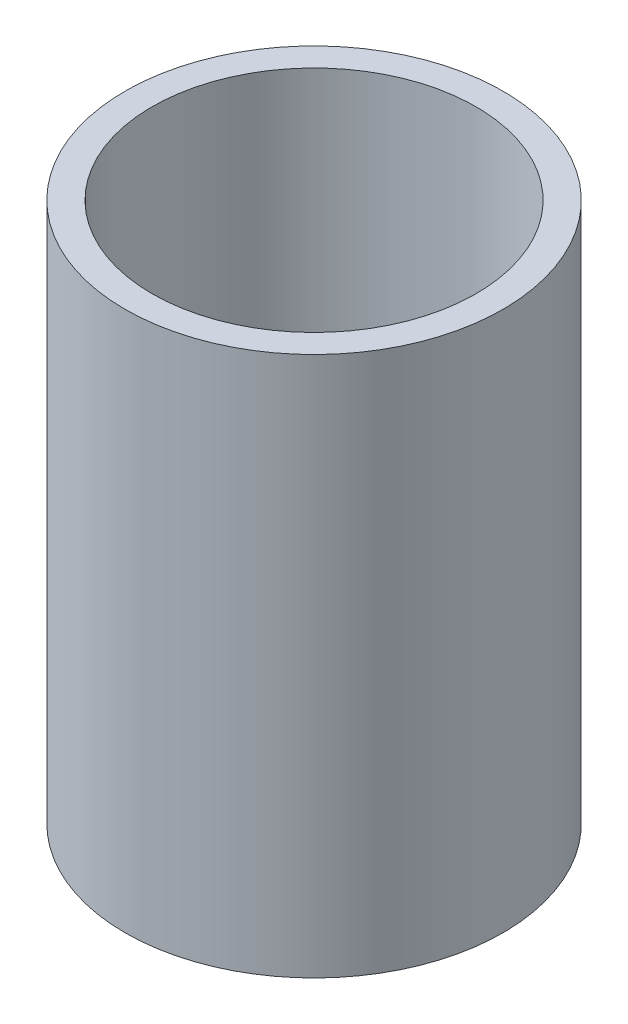
SolidWorks part; units mm, degrees
material "AISI 1035 钢 (SS)"
ref_plane "前视基准面" through (0, 0, 0) normal (0, 0, 1) x (1, 0, 0)
ref_plane "上视基准面" through (0, 0, 0) normal (0, 1, 0) x (1, 0, 0)
ref_plane "右视基准面" through (0, 0, 0) normal (1, 0, 0) x (0, 0, -1)
sketch "草图2" plane through (0, 0, 0) normal (0, 0, 1) x (1, 0, 0)
  line L1 (17.5, 0) -> (17.5, -50)
  line L4 (17.5, 0) -> (15, 0)
  line L5 (15, 0) -> (15, -50)
  line L6 (15, -50) -> (17.5, -50)
  line L7 (0, 0) -> (0, -50) construction
  dimension "D2" = 15
  dimension "D3" = 2.5
  dimension "D4" = 50
revolve "旋转1" add sketch "草图2" angle 360 about L7
